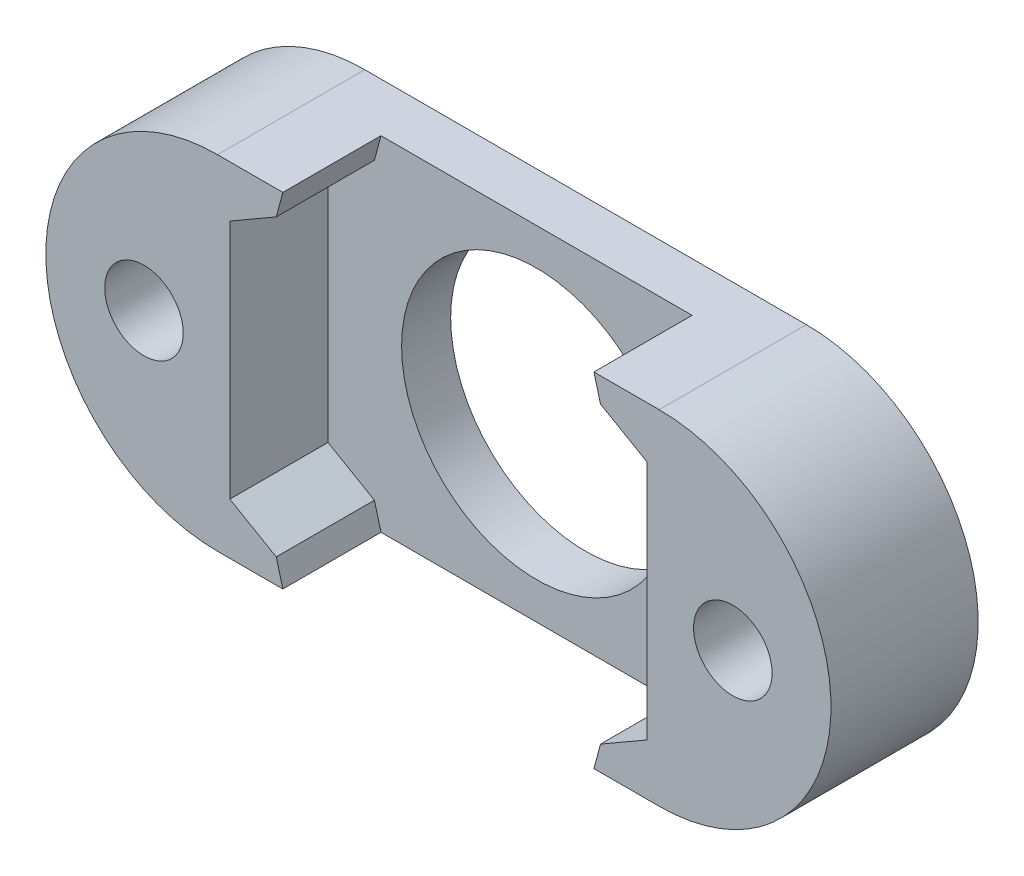
SolidWorks part; units mm, degrees
ref_plane "Plan de face" through (0, 0, 0) normal (0, 0, 1) x (1, 0, 0)
ref_plane "Plan de dessus" through (0, 0, 0) normal (0, 1, 0) x (1, 0, 0)
ref_plane "Plan de droite" through (0, 0, 0) normal (1, 0, 0) x (0, 0, -1)
sketch "Esquisse1" plane through (0, 0, 0) normal (0, 0, 1) x (1, 0, 0)
  line L0 (-27.2542, 0) -> (-9.2542, 0) construction
  line L1 (-27.2542, 7) -> (-9.2542, 7)
  line L2 (-27.2542, -7) -> (-9.2542, -7)
  arc A0 (-27.2542, 7) -> (-27.2542, -7) centre (-27.2542, 0) ccw
  arc A1 (-9.2542, -7) -> (-9.2542, 7) centre (-9.2542, 0) ccw
  point P3 (-18.2542, 0)
  dimension "D1" = 18
  dimension "D2" = 14
extrude "Boss.-Extru.1" add sketch "Esquisse1" along normal blind 6
sketch "Esquisse3" plane through (0, 0, 6) normal (0, 0, 1) x (1, 0, 0)
  line L0 (-27.2542, -7) -> (-9.2542, -7) construction
  circle A0 centre (-18.2542, 0) radius 5.5
  circle A1 centre (-30.2542, 0) radius 1.6
  circle A2 centre (-6.2542, 0) radius 1.6
  dimension "D1" = 3.2
  dimension "D2" = 3.2
  dimension "D5" = 11
  dimension "D3" = 24
  dimension "D4" = 12
  dimension "D6" = 7
  dimension "D7" = 9
  dimension "D8" = 7
  dimension "D9" = 7
extrude "Enlèv. mat.-Extru.1" cut sketch "Esquisse3" against normal through all
sketch "Esquisse4" plane through (0, 0, 6) normal (0, 0, 1) x (1, 0, 0)
  line L8 (-9.7542, -4.9075) -> (-9.7542, 4.9075)
  line L9 (-9.7542, 4.9075) -> (-18.2542, 9.815)
  line L10 (-18.2542, 9.815) -> (-26.7542, 4.9075)
  line L11 (-26.7542, 4.9075) -> (-26.7542, -4.9075)
  line L12 (-26.7542, -4.9075) -> (-18.2542, -9.815)
  line L13 (-18.2542, -9.815) -> (-9.7542, -4.9075)
  circle A1 centre (-18.2542, 0) radius 8.5 construction
  dimension "D2" = 17
extrude "Enlèv. mat.-Extru.2" cut sketch "Esquisse4" against normal blind 4
chamfer "Chamfer1" distance 2 angle 45 4 edges at (-13.3785, -7, 4) (-13.3785, 7, 4) (-23.1298, -7, 4) (-23.1298, 7, 4)
